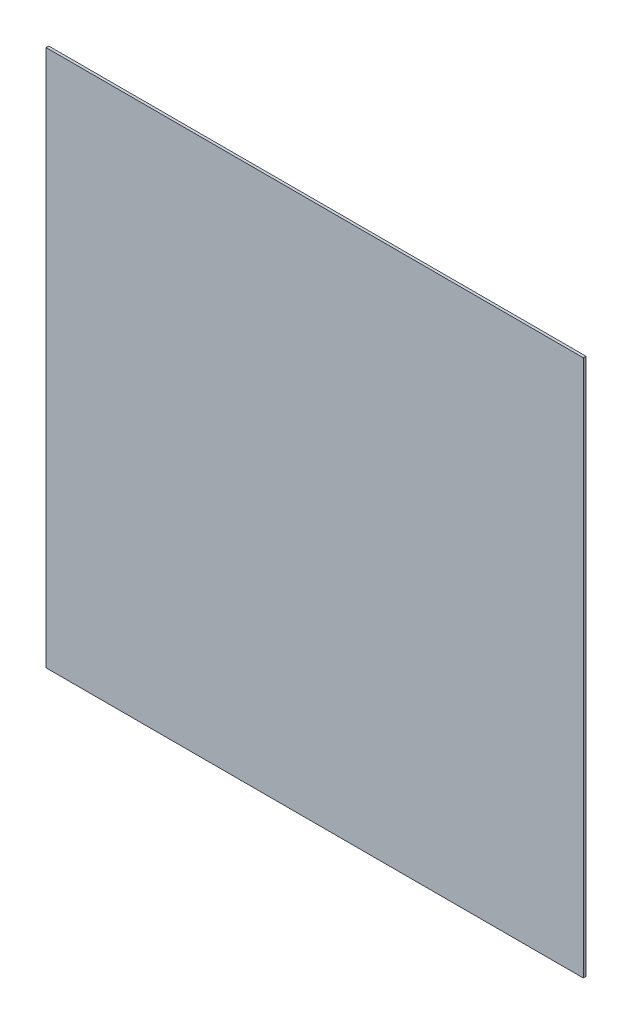
SolidWorks part; units mm, degrees
ref_plane "정면" through (0, 0, 0) normal (0, 0, 1) x (1, 0, 0)
ref_plane "윗면" through (0, 0, 0) normal (0, 1, 0) x (1, 0, 0)
ref_plane "우측면" through (0, 0, 0) normal (1, 0, 0) x (0, 0, -1)
sketch "스케치1" plane through (0, 0, 0) normal (0, 1, 0) x (1, 0, 0)
  line L1 (0, 0) -> (600, 0)
  line L2 (0, 0) -> (0, 3)
  line L3 (0, 3) -> (600, 3)
  line L4 (600, 0) -> (600, 3)
  dimension "D1" = 600
  dimension "D2" = 3
extrude "보스-돌출1" add sketch "스케치1" along normal blind 600
